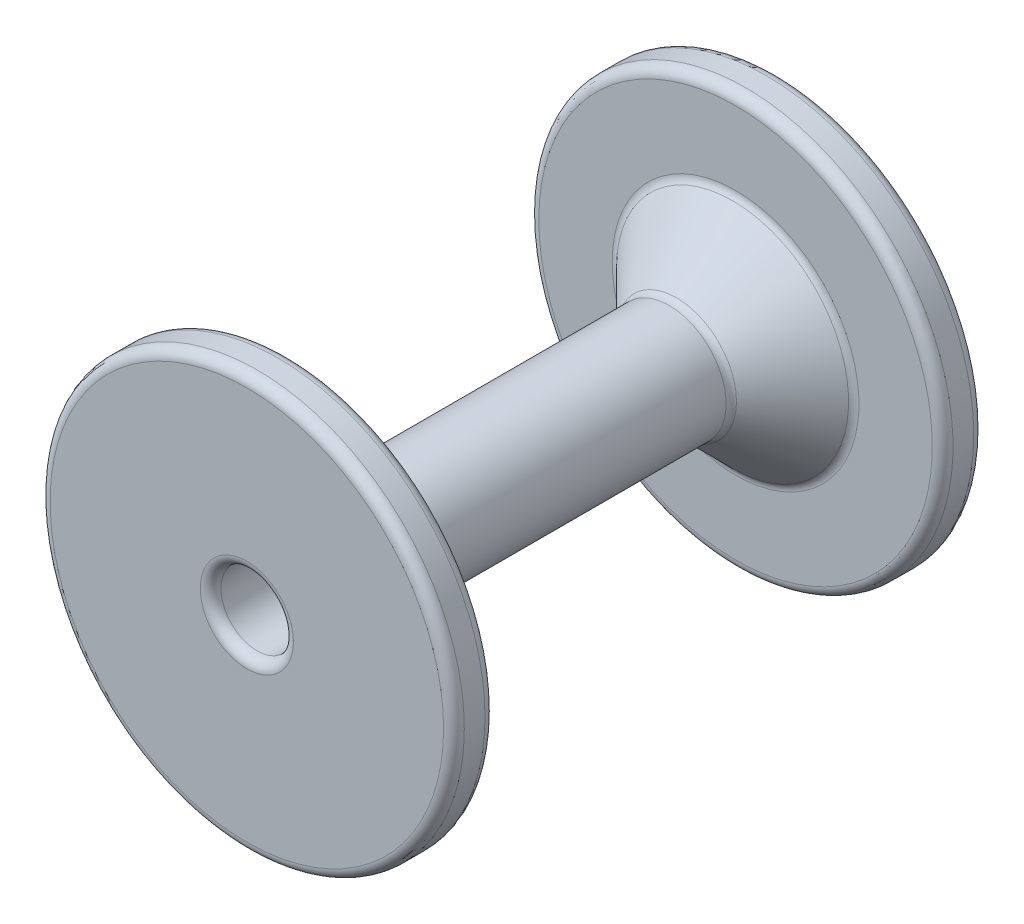
SolidWorks part; units mm, degrees
ref_plane "Front Plane" through (0, 0, 0) normal (0, 0, 1) x (1, 0, 0)
ref_plane "Top Plane" through (0, 0, 0) normal (0, 1, 0) x (1, 0, 0)
ref_plane "Right Plane" through (0, 0, 0) normal (1, 0, 0) x (0, 0, -1)
sketch "Sketch1" plane through (0, 0, 0) normal (0, 0, 1) x (1, 0, 0)
  circle A0 centre (0, 0) radius 1.75
  circle A1 centre (0, 0) radius 2.75
  dimension "D1" = 3.5
  dimension "D2" = 5.5
extrude "Boss-Extrude1" add sketch "Sketch1" along normal mid plane 25.6
sketch "Sketch2" plane through (0, 0, 12.8) normal (0, 0, 1) x (1, 0, 0)
  circle A0 centre (0, 0) radius 2.75 construction
  circle A1 centre (0, 0) radius 2.75
  circle A2 centre (0, 0) radius 10
  dimension "D1" = 20
extrude "Boss-Extrude2" add sketch "Sketch2" against normal blind 2
mirror "Mirror1" about plane through (0, 0, 0) normal (0, 0, 1) of "Boss-Extrude2"
chamfer "Chamfer3" distance 3 angle 45 1 edges at (-2.75, 0, -10.8)
sketch "Sketch4" plane through (0, 0, -12.8) normal (0, 0, -1) x (-1, 0, 0)
  line L1 (1.5877, 2.75) -> (-1.5877, 2.75)
  line L2 (-1.5877, 2.75) -> (-3.1754, 0)
  line L3 (-3.1754, 0) -> (-1.5877, -2.75)
  line L4 (-1.5877, -2.75) -> (1.5877, -2.75)
  line L5 (1.5877, -2.75) -> (3.1754, 0)
  line L6 (3.1754, 0) -> (1.5877, 2.75)
  circle A0 centre (0, 0) radius 2.75 construction
  dimension "D1" = 5.5
extrude "Cut-Extrude1" cut sketch "Sketch4" against normal blind 2.4
fillet "Fillet2" radius 0.5 14 edges at (10, 0, -10.8) (-5.75, 0, -10.8) (10, 0, 10.8) (2.75, 0, 10.8) (10, 0, -12.8) (2.3816, 1.375, -12.8) (2.3816, -1.375, -12.8) (0, -2.75, -12.8) (-2.3816, -1.375, -12.8) (-2.3816, 1.375, -12.8) (0, 2.75, -12.8) (10, 0, 12.8) (1.75, 0, 12.8) (-2.75, 0, -7.8)
